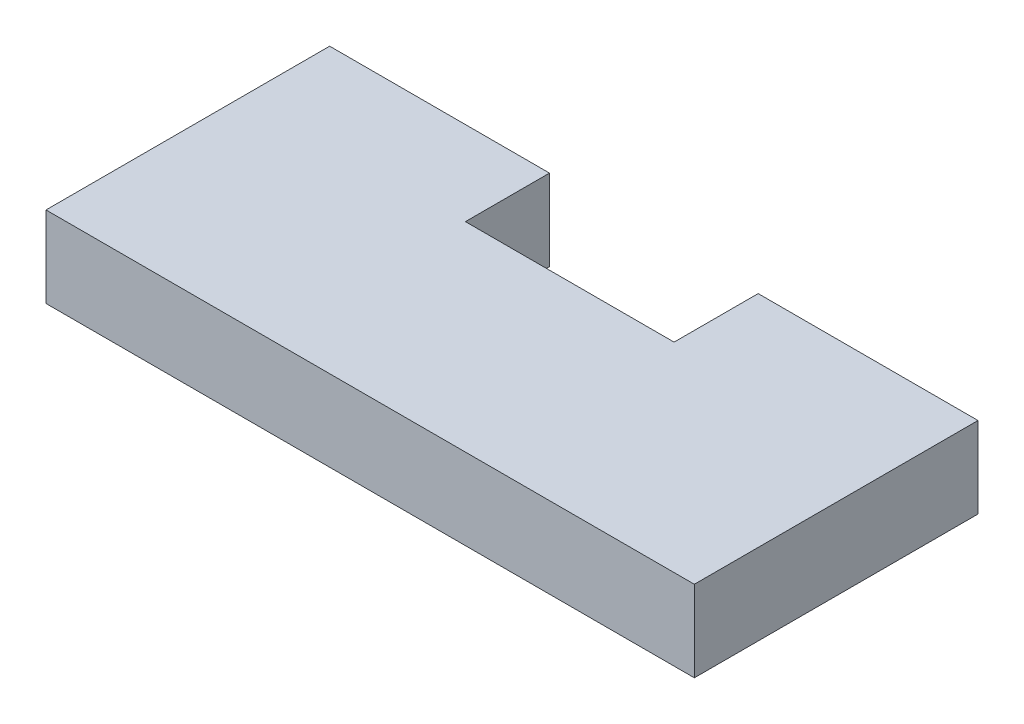
SolidWorks part; units mm, degrees
material "Acier S235"
ref_plane "Plan de face" through (0, 0, 0) normal (0, 0, 1) x (1, 0, 0)
ref_plane "Plan de dessus" through (0, 0, 0) normal (0, 1, 0) x (1, 0, 0)
ref_plane "Plan de droite" through (0, 0, 0) normal (1, 0, 0) x (0, 0, -1)
sketch "Esquisse1" plane through (0, 0, 0) normal (0, 1, 0) x (1, 0, 0)
  line L0 (-16, 0) -> (16, 0)
  line L1 (16, 0) -> (16, 14)
  line L2 (16, 14) -> (5.15, 14)
  line L3 (5.15, 14) -> (5.15, 9.85)
  line L4 (5.15, 9.85) -> (-5.15, 9.85)
  line L5 (-5.15, 9.85) -> (-5.15, 14)
  line L6 (-5.15, 14) -> (-16, 14)
  line L7 (-16, 14) -> (-16, 0)
  point P4 (0, 0)
  dimension "D1" = 10.3
  dimension "D2" = 10.85
  dimension "D3" = 10.85
  dimension "D4" = 14
  dimension "D5" = 4.15
extrude "Boss.-Extru.1" add sketch "Esquisse1" along normal blind 4
